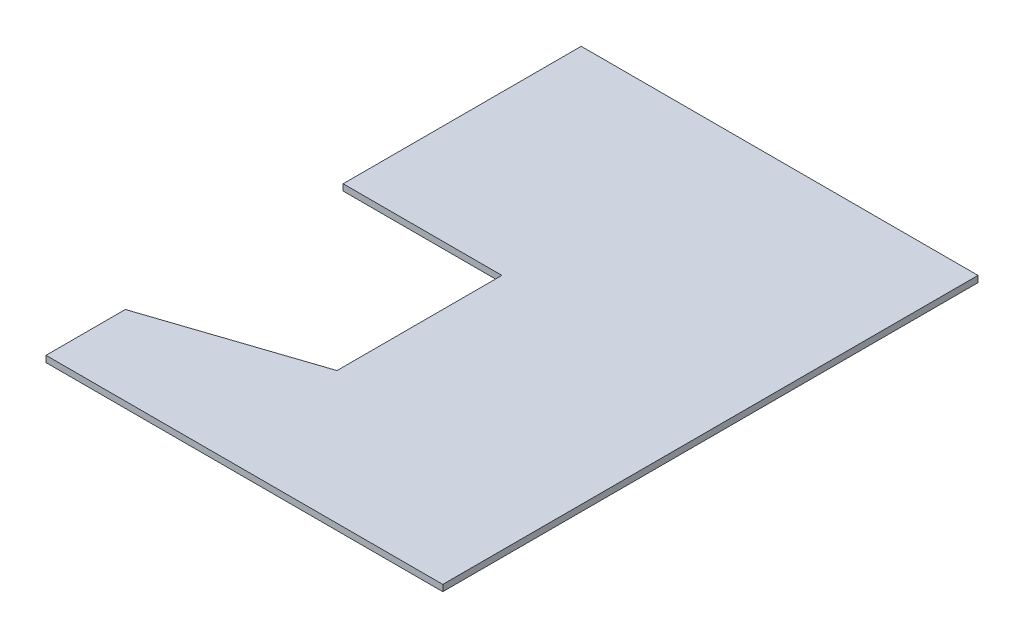
SolidWorks part; units mm, degrees
material "Cedar"
ref_plane "Front Plane" through (0, 0, 0) normal (0, 0, 1) x (1, 0, 0)
ref_plane "Top Plane" through (0, 0, 0) normal (0, 1, 0) x (1, 0, 0)
ref_plane "Right Plane" through (0, 0, 0) normal (1, 0, 0) x (0, 0, -1)
sketch "Sketch1" plane through (0, 0, 0) normal (0, 1, 0) x (1, 0, 0)
  line L0 (-216.2727, 122.7979) -> (383.7273, 122.7979) construction
  line L1 (383.7273, 122.7979) -> (383.7273, 22.7979) construction
  line L2 (383.7273, 22.7979) -> (-216.2727, -177.2021) construction
  line L3 (-216.2727, -177.2021) -> (-216.2727, 122.7979) construction
  line L4 (333.7273, 132.7979) -> (433.7273, 132.7979)
  line L5 (433.7273, 132.7979) -> (433.7273, 28.9237)
  line L6 (433.7273, 28.9237) -> (333.7273, -4.4097)
  line L7 (333.7273, -4.4097) -> (333.7273, -54.4097)
  line L8 (333.7273, -54.4097) -> (583.7273, -54.4097)
  line L9 (583.7273, -54.4097) -> (583.7273, 282.7979)
  line L10 (583.7273, 282.7979) -> (333.7273, 282.7979)
  line L11 (333.7273, 282.7979) -> (333.7273, 132.7979)
  dimension "D1" = 300
  dimension "D2" = 600
  dimension "D3" = 100
  dimension "D4" = 50
  dimension "D5" = 150
  dimension "D6" = 50
  dimension "D7" = 10
  dimension "D8" = 10
  dimension "D9" = 50
  dimension "D10" = 250
extrude "Boss-Extrude1" add sketch "Sketch1" along normal blind 4
